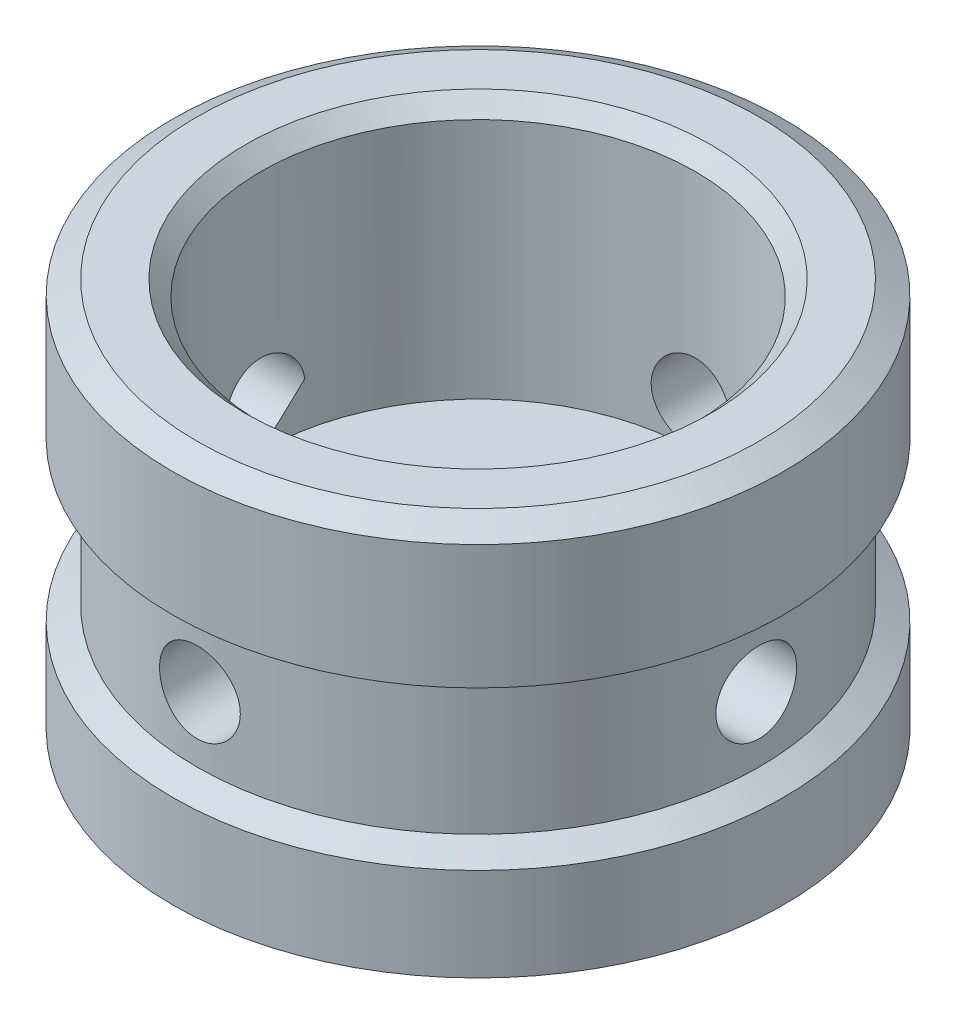
SolidWorks part; units mm, degrees
ref_plane "Front Plane" through (0, 0, 0) normal (0, 0, 1) x (1, 0, 0)
ref_plane "Top Plane" through (0, 0, 0) normal (0, 1, 0) x (1, 0, 0)
ref_plane "Right Plane" through (0, 0, 0) normal (1, 0, 0) x (0, 0, -1)
sketch "Sketch1" plane through (0, 0, 0) normal (0, 0, 1) x (1, 0, 0)
  line L0 (11.5, -7.62) -> (12.4975, -7.0441)
  line L1 (11.5, -7.62) -> (9.5, -7.62)
  line L2 (0, 8.89) -> (11.5, 8.89)
  line L3 (12.4975, -5.1391) -> (0, -5.1391) construction
  line L4 (0, 0) -> (11.5, 0) construction
  line L5 (11.5, 8.89) -> (12.4975, 8.3141)
  line L6 (9.5, -7.62) -> (9.5, -8.89)
  line L7 (9.5, -8.89) -> (0, -8.89)
  line L8 (0, 8.89) -> (0, -8.89) construction
  line L9 (0, 8.89) -> (0, -8.89) construction
  line L10 (12.4975, 8.3141) -> (12.4975, 3.2341)
  line L11 (12.4975, -7.0441) -> (12.4975, -3.2341)
  line L12 (12.4975, -3.2341) -> (11.5, -2.6582)
  line L13 (11.5, -2.6582) -> (11.5, 2.6582)
  line L14 (12.4975, 3.2341) -> (11.5, 2.6582)
  line L15 (12.4975, 5.7741) -> (0, 5.7741) construction
  line L16 (0, 8.89) -> (0, -8.89)
  dimension "D8" = 17.78
  dimension "D1" = 23
  dimension "D2" = 9.5
  dimension "D3" = 30
  dimension "D4" = 24.9949
  dimension "D5" = 1.27
  dimension "D6" = 3.81
  dimension "D7" = 30
revolve "Revolve1" add sketch "Sketch1" angle 360 about L8
sketch "Sketch2" plane through (0, 0, 0) normal (1, 0, 0) x (0, 0, -1)
  circle A0 centre (0, 0) radius 1.651
  dimension "D1" = 3.302
extrude "Cut-Extrude1" cut sketch "Sketch2" against normal up to next (11.5 mm away)
pattern_circular "CirPattern1" count 4 over 360 about axis through (0, 8.89, 0) along (0, 1, 0) of "Cut-Extrude1"
sketch "Sketch3" plane through (0, 8.89, 0) normal (0, 1, 0) x (1, 0, 0)
  circle A0 centre (0, 0) radius 8.89
  dimension "D1" = 17.78
extrude "Cut-Extrude3" cut sketch "Sketch3" against normal blind 10.541
sketch "Sketch4" plane through (0, -8.89, 0) normal (0, -1, 0) x (1, 0, 0)
  circle A0 centre (0, 0) radius 8.89 construction
  circle A1 centre (0, 0) radius 8.89
extrude "Cut-Extrude4" cut sketch "Sketch4" against normal blind 1.27
chamfer "Chamfer1" distance 0.635 angle 45 1 edges at (-8.89, 8.89, 0)
